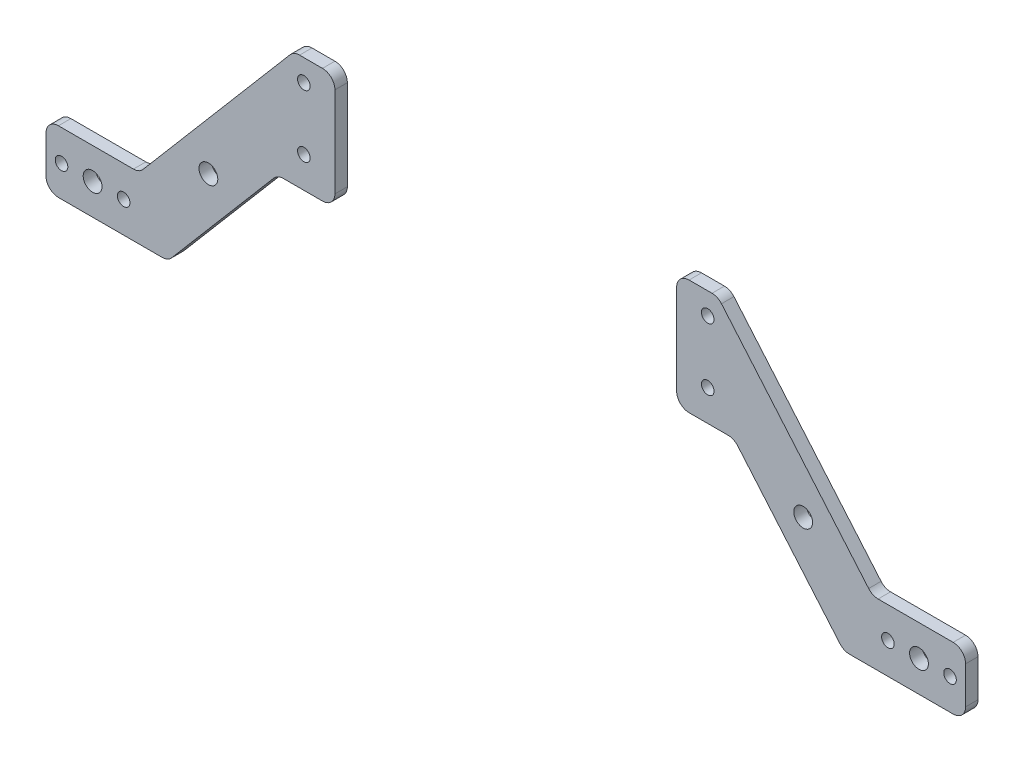
SolidWorks part; units mm, degrees
material "Thornel Mat VMA"
ref_plane "前视基准面" through (0, 0, 0) normal (0, 0, 1) x (1, 0, 0)
ref_plane "上视基准面" through (0, 0, 0) normal (0, 1, 0) x (1, 0, 0)
ref_plane "右视基准面" through (0, 0, 0) normal (1, 0, 0) x (0, 0, -1)
other "Configuration Table"
sketch "草图1" plane through (0, 0, 0) normal (0, 0, 1) x (1, 0, 0)
  line L0 (-143, -51.5) -> (-133, -51.5) construction
  line L1 (-65, -10) -> (65, -10) construction
  line L2 (-65, -10) -> (-65, 10) construction
  line L3 (-65, 10) -> (65, 10) construction
  line L4 (65, -10) -> (65, 10) construction
  line L5 (-65, -10) -> (65, 10) construction
  line L6 (-65, 10) -> (65, -10) construction
  line L7 (-133, -51.5) -> (-123, -51.5) construction
  line L8 (0, 0) -> (0, -50000) construction
  line L9 (-118, -61.5) -> (-108.756, -61.5)
  line L10 (-148, -61.5) -> (-118, -61.5)
  line L11 (-148, -61.5) -> (-148, -41.5)
  line L12 (-148, -41.5) -> (-118, -41.5)
  line L13 (-118, -61.5) -> (-118, -41.5)
  line L14 (-148, -61.5) -> (-118, -41.5) construction
  line L15 (-148, -41.5) -> (-118, -61.5) construction
  line L16 (-73.4529, -20) -> (73.4529, -20)
  line L17 (-118, -41.5) -> (-68.2354, 17)
  line L18 (-68.2354, 17) -> (68.2354, 17)
  line L19 (-108.756, -61.5) -> (-73.4529, -20)
  line L20 (-47.5, -8.5) -> (47.5, -8.5) construction
  line L21 (-47.5, -8.5) -> (-47.5, 16.5) construction
  line L22 (-47.5, 16.5) -> (47.5, 16.5) construction
  line L23 (47.5, -8.5) -> (47.5, 16.5) construction
  line L24 (-47.5, -8.5) -> (47.5, 16.5) construction
  line L25 (-47.5, 16.5) -> (47.5, -8.5) construction
  line L26 (148, -41.5) -> (118, -61.5) construction
  line L27 (148, -61.5) -> (118, -41.5) construction
  line L28 (133, -51.5) -> (123, -51.5) construction
  line L29 (143, -51.5) -> (133, -51.5) construction
  line L30 (118, -61.5) -> (118, -41.5)
  line L31 (148, -41.5) -> (118, -41.5)
  line L32 (148, -61.5) -> (148, -41.5)
  line L33 (148, -61.5) -> (118, -61.5)
  line L34 (118, -61.5) -> (108.756, -61.5)
  line L35 (118, -41.5) -> (68.2354, 17)
  line L36 (108.756, -61.5) -> (73.4529, -20)
  line L37 (-118, -41.5) -> (-108.756, -61.5) construction
  line L38 (-73.4529, -20) -> (-82.6969, 0) construction
  line L39 (-78.0749, -10) -> (-113.378, -51.5) construction
  circle A4 centre (-65, 10) radius 2.025
  circle A5 centre (-65, -10) radius 2.025
  circle A6 centre (65, 10) radius 2.025
  circle A7 centre (65, -10) radius 2.025
  circle A8 centre (-143, -51.5) radius 2.025
  circle A9 centre (-123, -51.5) radius 2.025
  circle A10 centre (-133, -51.5) radius 3.025
  circle A11 centre (143, -51.5) radius 2.025
  circle A12 centre (133, -51.5) radius 3.025
  circle A13 centre (123, -51.5) radius 2.025
  circle A14 centre (-47.5, 16.5) radius 2.025
  circle A15 centre (-47.5, -8.5) radius 2.025
  circle A16 centre (47.5, 16.5) radius 2.025
  circle A17 centre (47.5, -8.5) radius 2.025
  circle A18 centre (-65, 10) radius 7 construction
  circle A19 centre (133, -51.5) radius 3.025
  circle A20 centre (123, -51.5) radius 2.025
  circle A21 centre (143, -51.5) radius 2.025
  circle A22 centre (-95.7264, -30.75) radius 3.025
  circle A23 centre (95.7264, -30.75) radius 3.025
  point P0 (0, 0)
  point P29 (0, 17)
  point P31 (0, 4)
  point P54 (0, -20)
  dimension "D1" = 130
  dimension "D3" = 4.05
  dimension "D5" = 6.05
  dimension "D6" = 58
  dimension "D7" = 41.5
  dimension "D8" = 5
  dimension "D10" = 10
  dimension "D16" = 6.05
  dimension "D2" = 20
  dimension "D4" = 20
  dimension "D9" = 20
  dimension "D11" = 25
  dimension "D12" = 95
  dimension "D13" = 78
  dimension "D14" = 20
  dimension "D15" = 7
extrude "凸台-拉伸1" add sketch "草图1" along normal blind 4 contours L10 L13 L12 L11 A10 A9 A8 | L36 L34 L30 L35 L18 L17 L13 L9 L19 L16 A17 A16 A15 A14 A7 A6 A5 A4 | L33 L32 L31 L30 A12 A11 A13
sketch "草图2" plane through (0, 0, 4) normal (0, 0, 1) x (1, 0, 0)
  line L1 (47.5, -8.5) -> (-47.5, -8.5) construction
  line L2 (47.5, -8.5) -> (47.5, 16.5) construction
  line L3 (47.5, 16.5) -> (-47.5, 16.5) construction
  line L4 (-47.5, -8.5) -> (-47.5, 16.5) construction
  line L5 (47.5, -8.5) -> (-47.5, 16.5) construction
  line L6 (47.5, 16.5) -> (-47.5, -8.5) construction
  line L7 (-39.5, -14) -> (39.5, -14)
  line L8 (-39.5, -14) -> (-39.5, 22)
  line L9 (-39.5, 22) -> (39.5, 22)
  line L10 (39.5, -14) -> (39.5, 22)
  line L11 (-39.5, -14) -> (39.5, 22) construction
  line L12 (-39.5, 22) -> (39.5, -14) construction
  line L13 (-73.4529, -20) -> (73.4529, -20) construction
  point P0 (0, 4)
  point P10 (0, 4)
  dimension "D1" = 8
  dimension "D2" = 6
extrude "切除-拉伸1" cut sketch "草图2" against normal blind 4
fillet "圆角1" radius 4 14 edges at (39.5, -14, 2) (-39.5, -14, 2) (-148, -61.5, 2) (-148, -41.5, 2) (-118, -41.5, 2) (-68.2354, 17, 2) (118, -41.5, 2) (148, -41.5, 2) (148, -61.5, 2) (108.756, -61.5, 2) (73.4529, -20, 2) (-73.4529, -20, 2) (-108.756, -61.5, 2) (68.2354, 17, 2)
sketch "草图3" plane through (0, 0, 4) normal (0, 0, 1) x (1, 0, 0)
  line L1 (-66.3866, 17) -> (-49.4623, 17) construction
  line L5 (-55, -17) -> (-55, 17) construction
  line L8 (-71.6041, -20) -> (71.6041, -20) construction
  line L9 (55, -17) -> (-55, -17)
  line L10 (55, -17) -> (55, 17)
  line L11 (55, 17) -> (-55, 17)
  line L12 (-55, -17) -> (-55, 17)
  line L13 (55, -17) -> (-55, 17) construction
  line L14 (55, 17) -> (-55, -17) construction
  line L16 (-55, -17) -> (-55, -20)
  line L17 (-55, -20) -> (55, -20)
  line L18 (55, -17) -> (55, -20)
  point P11 (0, 0)
  dimension "D1" = 110
extrude "切除-拉伸2" cut sketch "草图3" against normal blind 10
fillet "圆角2" radius 4 2 edges at (-55, 17, 2) (-55, -20, 2)
fillet "圆角3" radius 4 2 edges at (55, 17, 2) (55, -20, 2)
